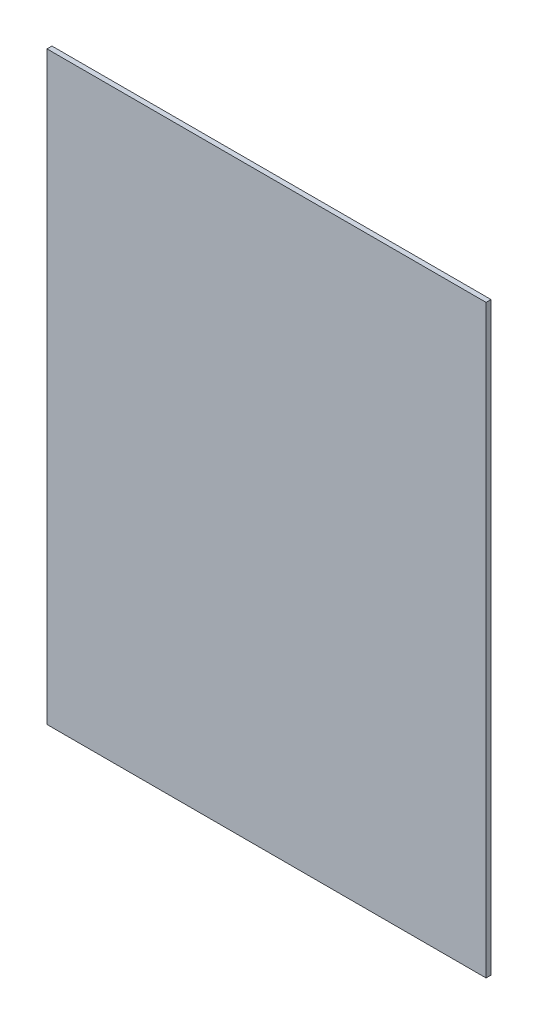
SolidWorks part; units mm, degrees
ref_plane "Plan de face" through (0, 0, 0) normal (0, 0, 1) x (1, 0, 0)
ref_plane "Plan de dessus" through (0, 0, 0) normal (0, 1, 0) x (1, 0, 0)
ref_plane "Plan de droite" through (0, 0, 0) normal (1, 0, 0) x (0, 0, -1)
sketch "Esquisse1" plane through (0, 0, 0) normal (0, 0, 1) x (1, 0, 0)
  line L1 (0, 0) -> (88.7, 0)
  line L2 (0, 0) -> (0, 118.2)
  line L3 (0, 118.2) -> (88.7, 118.2)
  line L4 (88.7, 0) -> (88.7, 118.2)
  dimension "D1" = 118.2
  dimension "D2" = 88.7
extrude "Boss.-Extru.1" add sketch "Esquisse1" along normal blind 1
sketch "Esquisse2" plane through (0, 0, 1) normal (0, 0, 1) x (1, 0, 0)
  line L0 (88.7, 0) -> (88.7, 118.2) construction
  line L1 (65.7, 135.9) -> (11.7, 135.9)
  line L2 (65.7, 135.9) -> (65.7, 33.9)
  line L3 (65.7, 33.9) -> (11.7, 33.9)
  line L4 (11.7, 135.9) -> (11.7, 33.9)
  line L6 (0, 0) -> (88.7, 0) construction
  dimension "D1" = 102
  dimension "D2" = 54
  dimension "D3" = 23
  dimension "D4" = 33.9
